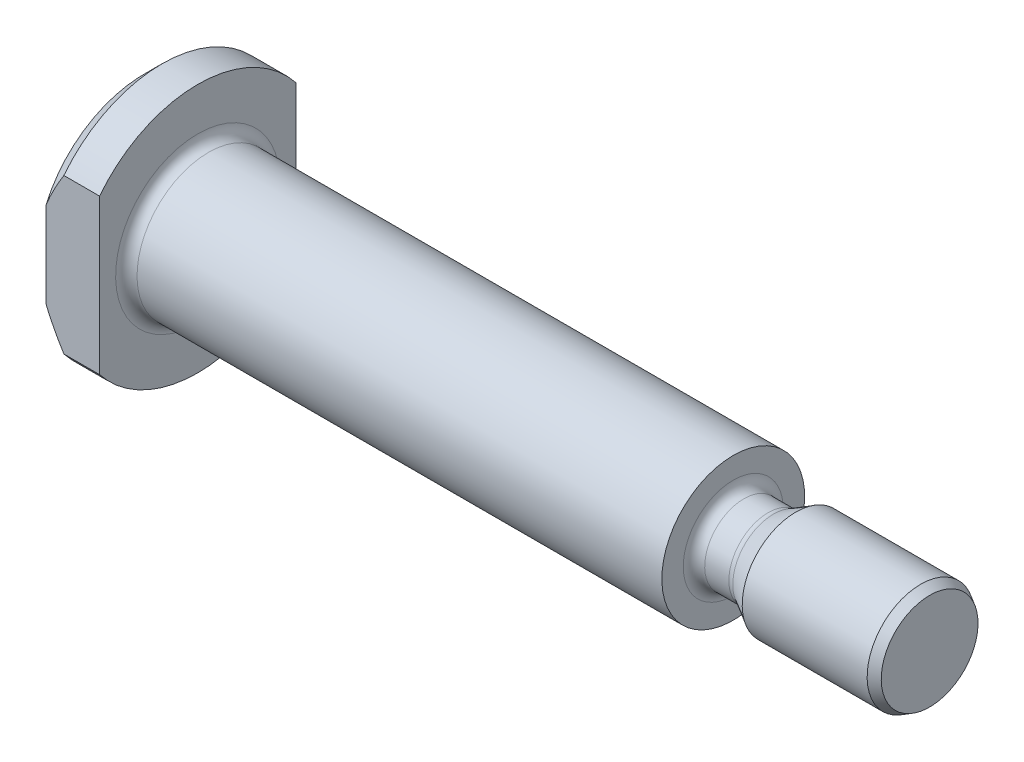
SolidWorks part; units mm, degrees
ref_plane "Ebene vorne" through (0, 0, 0) normal (0, 0, 1) x (1, 0, 0)
ref_plane "Ebene oben" through (0, 0, 0) normal (0, 1, 0) x (1, 0, 0)
ref_plane "Ebene rechts" through (0, 0, 0) normal (1, 0, 0) x (0, 0, -1)
sketch "Skizze1" plane through (0, 0, 0) normal (0, 0, 1) x (1, 0, 0)
  line L0 (-3, 0) -> (-3, 6)
  line L1 (55, 0) -> (-55, 0) construction
  line L2 (-2, 7) -> (0, 7)
  line L3 (0, -55) -> (0, 55) construction
  line L4 (0, 7) -> (0, 4)
  line L5 (0, 4) -> (30, 4)
  line L6 (30, 4) -> (30, 2.2)
  line L7 (30, 2.2) -> (32.1144, 2.2)
  line L8 (32.1144, 2.2) -> (33.5, 3)
  line L9 (33.5, 3) -> (40.5, 3)
  line L12 (41, 0) -> (-3, 0)
  line L13 (-2, 7) -> (-3, 6)
  line L15 (41, 0) -> (41, 2.7113)
  line L17 (40.5, 3) -> (41, 2.7113)
  dimension "D1" = 7
  dimension "D2" = 4
  dimension "D3" = 3
  dimension "D4" = 30
  dimension "D6" = 3
  dimension "D7" = 1
  dimension "D8" = 135
  dimension "D9" = 2.2
  dimension "D5" = 3.5
  dimension "D10" = 30
  dimension "D12" = 11
  dimension "D13" = 0.5
  dimension "D11" = 150
revolve "Rotation1" add sketch "Skizze1" angle 360 about L12
sketch "Skizze3" plane through (0, 0, 0) normal (1, 0, 0) x (0, 0, -1)
  line L0 (55, 0) -> (-55, 0) construction
  line L5 (-5.5, -7) -> (-7, -7)
  line L6 (-5.5, -7) -> (-5.5, 7)
  line L7 (-5.5, 7) -> (-7, 7)
  line L8 (-7, -7) -> (-7, 7)
  line L9 (-5.5, -7) -> (-7, 7) construction
  line L10 (-5.5, 7) -> (-7, -7) construction
  line L11 (0, 7.689) -> (0, -7.6816) construction
  line L12 (7, -7) -> (5.5, -7)
  line L13 (7, -7) -> (7, 7)
  line L14 (7, 7) -> (5.5, 7)
  line L15 (5.5, -7) -> (5.5, 7)
  line L16 (7, -7) -> (5.5, 7) construction
  line L17 (7, 7) -> (5.5, -7) construction
  line L18 (0, 55) -> (0, -55) construction
  circle A1 centre (0, 0) radius 7 construction
  point P1 (-6.25, 0)
  point P8 (6.25, 0)
  dimension "D1" = 11
extrude "Schnitt-Linear austragen2" cut sketch "Skizze3" against normal up to surface (3 mm away) up to face at (-3, 6, 0)
fillet "Verrundung1" radius 0.6 1 edges at (0, 4, 0)
fillet "Verrundung3" radius 0.6 2 edges at (32.1144, 2.2, 0) (30, 2.2, 0)
equation "\"diameter\"= 8"
equation "\"length\"= 30"
equation "\"head_diameter\"= 14"
equation "\"head_thickness\"= 3"
equation "\"wrench_size\"= 11"
equation "\"radius\"= 0.6"
equation "\"chamfer_height\"= 1"
equation "\"thread_diameter\"= 6"
equation "\"thread_length\"= 11"
equation "\"undercut_diameter\"= 4.4"
equation "\"undercut_length\"= 3.5"
equation "\"undercut_radius\"= 0.6"
equation "\"D2@Skizze1\"= \"diameter\" / 2"
equation "\"D4@Skizze1\"= \"length\""
equation "\"D1@Skizze1\"= \"head_diameter\" / 2"
equation "\"D3@Skizze1\"= \"head_thickness\""
equation "\"D1@Skizze3\"= \"wrench_size\""
equation "\"D1@Verrundung1\"= \"radius\""
equation "\"D7@Skizze1\"= \"chamfer_height\""
equation "\"D6@Skizze1\"= \"thread_diameter\" / 2"
equation "\"D12@Skizze1\"= \"thread_length\""
equation "\"D9@Skizze1\"= \"undercut_diameter\" / 2"
equation "\"D5@Skizze1\"= \"undercut_length\""
equation "\"D1@Verrundung3\"= \"undercut_radius\""
